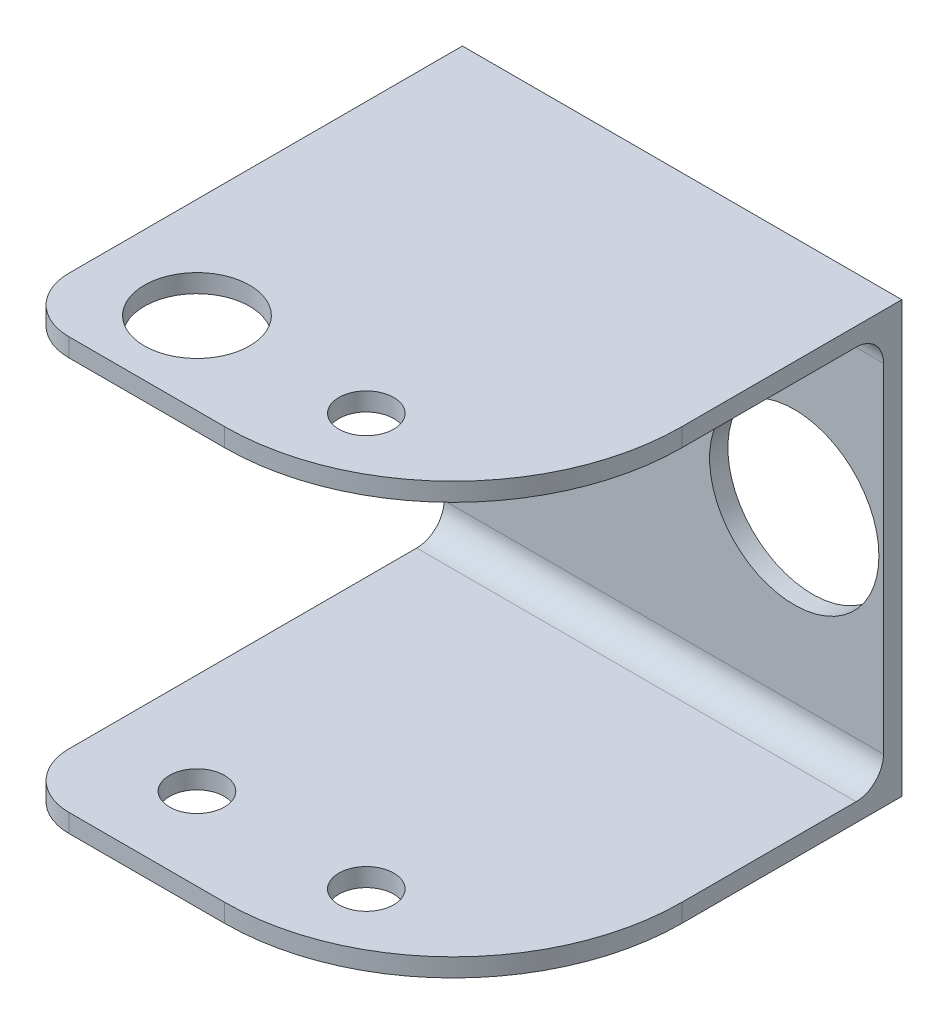
SolidWorks part; units mm, degrees
ref_plane "Front Plane" through (0, 0, 0) normal (0, 0, 1) x (1, 0, 0)
ref_plane "Top Plane" through (0, 0, 0) normal (0, 1, 0) x (1, 0, 0)
ref_plane "Right Plane" through (0, 0, 0) normal (1, 0, 0) x (0, 0, -1)
sketch "Sketch1" plane through (0, 0, 0) normal (0, 0, 1) x (1, 0, 0)
  line L1 (-24, 23.5) -> (24, 23.5)
  line L2 (-24, 23.5) -> (-24, -23.5)
  line L3 (-24, -23.5) -> (24, -23.5)
  line L4 (24, 23.5) -> (24, -23.5)
  line L5 (-24, 23.5) -> (24, -23.5) construction
  line L6 (-24, -23.5) -> (24, 23.5) construction
  point P0 (0, 0)
  dimension "D1" = 47
  dimension "D2" = 48
extrude "Boss-Extrude1" add sketch "Sketch1" along normal blind 49
sketch "Sketch3" plane through (24, 0, 0) normal (1, 0, 0) x (0, 0, -1)
  line L0 (-49, 23.5) -> (0, 23.5) construction
  line L1 (-2, 21.5) -> (-52, 21.5)
  line L2 (-2, 21.5) -> (-2, -21.5)
  line L3 (-2, -21.5) -> (-52, -21.5)
  line L4 (-52, 21.5) -> (-52, -21.5)
  line L5 (-49, -23.5) -> (0, -23.5) construction
  line L6 (0, -23.5) -> (0, 23.5) construction
  dimension "D1" = 2
  dimension "D2" = 2
  dimension "D3" = 2
  dimension "D4" = 50
extrude "Cut-Extrude1" cut sketch "Sketch3" against normal blind 49
sketch "Sketch4" plane through (0, 0, 2) normal (0, 0, 1) x (1, 0, 0)
  line L0 (-24, 21.5) -> (24, 21.5) construction
  line L1 (-24, -21.5) -> (-2, -21.5) construction
  line L2 (-24, -21.5) -> (-24, 21.5) construction
  line L3 (-24, 21.5) -> (-2, 21.5) construction
  line L4 (-2, -21.5) -> (-2, 21.5) construction
  circle A0 centre (14.25, 0) radius 9.25
  dimension "D1" = 18.5
  dimension "D2" = 16.25
  dimension "D3" = 22
extrude "Cut-Extrude2" cut sketch "Sketch4" against normal blind 2 contours A0
sketch "Sketch5" plane through (0, 23.5, 0) normal (0, 1, 0) x (1, 0, 0)
  line L0 (0, -1000) -> (0, 49000) construction
  line L1 (-24, -1000) -> (-24, 49000) construction
  line L2 (-2, -1012.3048) -> (-2, 48987.6952) construction
  line L3 (-1000, -40) -> (49000, -40) construction
  line L4 (24, -49) -> (-24, -49) construction
  circle A1 centre (-13, -40) radius 5.75
  circle A2 centre (5.5, -40) radius 3
  dimension "D2" = 9
  dimension "D3" = 11
  dimension "D4" = 11.5
  dimension "D5" = 6
  dimension "D1" = 22
  dimension "D6" = 18.5
extrude "Cut-Extrude3" cut sketch "Sketch5" against normal blind 2
sketch "Sketch7" plane through (0, -21.5, 0) normal (0, 1, 0) x (1, 0, 0)
  circle A0 centre (5.5, -40) radius 3
  circle A1 centre (-13, -40) radius 3
  dimension "D1" = 6
extrude "Cut-Extrude4" cut sketch "Sketch7" against normal blind 2
fillet "Fillet1" radius 25 2 edges at (24, 22.5, 49) (24, -22.5, 49)
fillet "Fillet2" radius 6 2 edges at (-24, -22.5, 49) (-24, 22.5, 49)
fillet "Fillet3" radius 3 2 edges at (0, 21.5, 2) (0, -21.5, 2)
